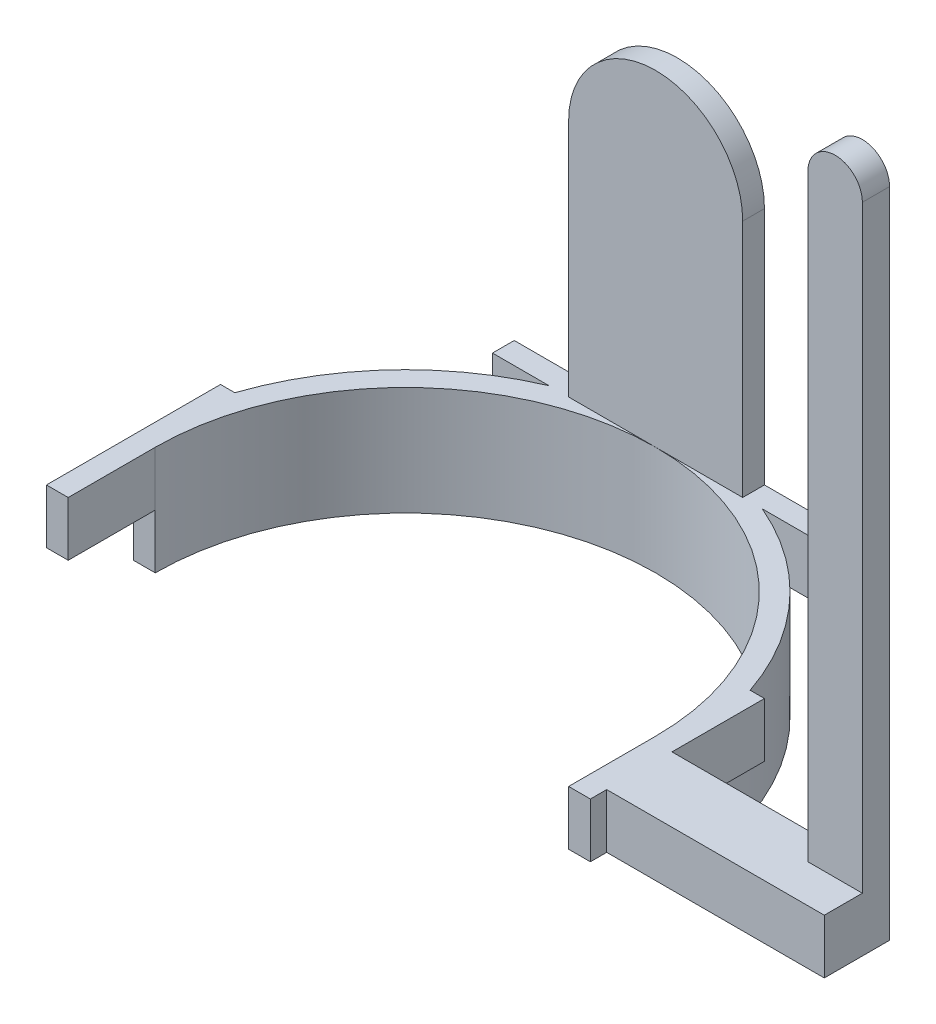
SolidWorks part; units mm, degrees
ref_plane "Front" through (0, 0, 0) normal (0, 0, 1) x (1, 0, 0)
ref_plane "Top" through (0, 0, 0) normal (0, 1, 0) x (1, 0, 0)
ref_plane "Right" through (0, 0, 0) normal (1, 0, 0) x (0, 0, -1)
sketch "草图1" plane through (0, 0, 0) normal (0, 1, 0) x (1, 0, 0)
  line L0 (-39.7033, 0) -> (64.2421, 0) construction
  line L1 (-50, 0) -> (-46, 0)
  line L2 (46, 0) -> (50, 0)
  arc A0 (-50, 0) -> (50, 0) centre (0, 0) cw
  arc A1 (-46, 0) -> (46, 0) centre (0, 0) cw
extrude "凸台-拉伸1" add sketch "草图1" along normal blind 10
sketch "草图3" plane through (0, 10, 0) normal (0, 1, 0) x (1, 0, 0)
  line L0 (46, 0) -> (50, 0) construction
  line L1 (-50, 0) -> (-46, 0) construction
  line L2 (-50, 16) -> (-47.3709, 16)
  line L3 (-50, 16) -> (-50, -16)
  line L4 (-50, -16) -> (-46, -16)
  line L5 (-46, 0) -> (-46, -16)
  line L6 (50, 16) -> (47.3709, 16)
  line L7 (50, 16) -> (50, -16)
  line L8 (50, -16) -> (46, -16)
  line L9 (46, 0) -> (46, -16)
  line L10 (0, 0) -> (0, 56.0177) construction
  line L11 (-26.9117, 46) -> (-19.5959, 46) construction
  line L12 (-22.8935, 50) -> (37.5767, 50) construction
  line L13 (19.5959, 46) -> (38.2628, 46) construction
  line L14 (-30, 50) -> (30, 50)
  line L15 (-30, 50) -> (-30, 46)
  line L16 (-30, 46) -> (-19.5959, 46)
  line L17 (30, 50) -> (30, 46)
  line L18 (19.5959, 46) -> (30, 46)
  arc A0 (-47.3709, 16) -> (-19.5959, 46) centre (0, 0) cw
  arc A1 (-46, 0) -> (46, 0) centre (0, 0) cw
  arc A2 (19.5959, 46) -> (47.3709, 16) centre (0, 0) cw
  dimension "D1" = 32
  dimension "D2" = 16
  dimension "D3" = 32
  dimension "D4" = 16
  dimension "D5" = 60
  dimension "D6" = 30
extrude "凸台-拉伸2" add sketch "草图3" along normal blind 10
sketch "草图4" plane through (0, 20, 0) normal (0, 1, 0) x (1, 0, 0)
  line L5 (0, 50) -> (0, 35.5033) construction
  line L6 (30, 50) -> (-30, 50) construction
  line L8 (-16, 50) -> (16, 50)
  line L9 (-16, 50) -> (-16, 46)
  line L10 (-16, 46) -> (16, 46)
  line L11 (16, 50) -> (16, 46)
  dimension "D1" = 16
  dimension "D2" = 16
extrude "凸台-拉伸3" add sketch "草图4" along normal blind 60
sketch "草图5" plane through (0, 0, -50) normal (0, 0, -1) x (-1, 0, 0)
  line L2 (-16, 64) -> (-16, 97.9053)
  line L3 (-16, 97.9053) -> (16, 97.9053)
  line L4 (16, 64) -> (16, 97.9053)
  arc A0 (16, 64) -> (-16, 64) centre (0, 64) ccw
extrude "切除-拉伸1" cut sketch "草图5" against normal blind 30
sketch "草图6" plane through (50, 0, 0) normal (1, 0, 0) x (0, 0, -1)
  line L0 (-16, 20) -> (16, 20) construction
  line L1 (-13, 20) -> (-1, 20)
  line L2 (-13, 20) -> (-13, 10)
  line L3 (-13, 10) -> (-1, 10)
  line L4 (-1, 20) -> (-1, 10)
  line L5 (-16, 10) -> (0, 10) construction
  line L6 (0, 10) -> (0, 0) construction
  dimension "D1" = 13
  dimension "D2" = 12
extrude "凸台-拉伸4" add sketch "草图6" along normal blind 40
sketch "草图7" plane through (0, 20, 0) normal (0, 1, 0) x (1, 0, 0)
  line L1 (90, -1) -> (80, -1)
  line L2 (90, -1) -> (90, -6)
  line L3 (90, -6) -> (80, -6)
  line L4 (80, -1) -> (80, -6)
  dimension "D1" = 5
  dimension "D2" = 10
extrude "凸台-拉伸5" add sketch "草图7" along normal blind 110
sketch "草图8" plane through (0, 0, 1) normal (0, 0, -1) x (-1, 0, 0)
  line L0 (-90, 130) -> (-80, 130) construction
  circle A0 centre (-85, 130) radius 5
extrude "凸台-拉伸6" add sketch "草图8" against normal blind 5
